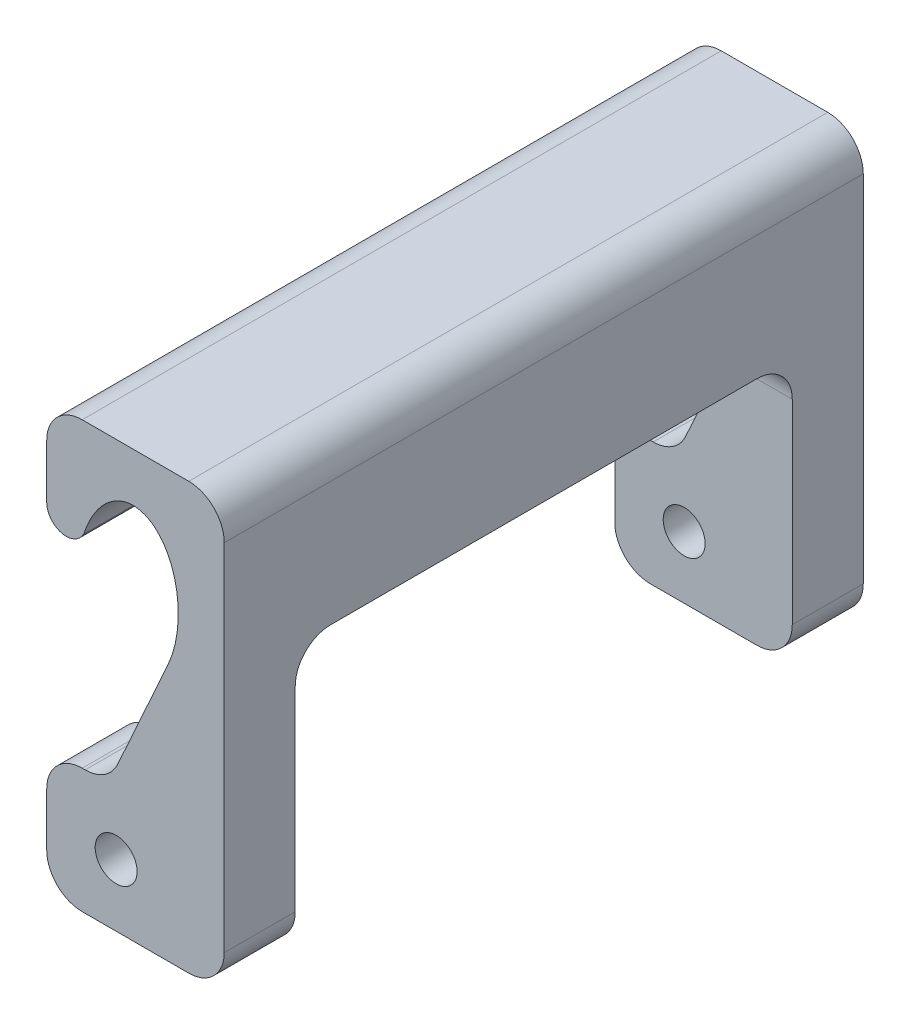
SolidWorks part; units mm, degrees
ref_plane "Front Plane" through (0, 0, 0) normal (0, 0, 1) x (1, 0, 0)
ref_plane "Top Plane" through (0, 0, 0) normal (0, 1, 0) x (1, 0, 0)
ref_plane "Right Plane" through (0, 0, 0) normal (1, 0, 0) x (0, 0, -1)
sketch "Sketch1" plane through (0, 0, 0) normal (0, 0, 1) x (1, 0, 0)
  line L0 (8.6779, 18.3764) -> (5.067, 10.3842)
  line L1 (2.54, 0) -> (10.16, 0)
  line L2 (0, 2.54) -> (0, 6.35)
  line L3 (2.54, 30.48) -> (10.16, 30.48)
  line L4 (12.7, 2.54) -> (12.7, 27.94)
  line L5 (2.7522, 8.89) -> (2.54, 8.89)
  line L6 (0, 24.08) -> (0, 27.94)
  arc A0 (0, 24.08) -> (2.5803, 23.349) centre (1.3937, 24.08) ccw
  arc A1 (2.5803, 23.349) -> (9.3645, 22.7915) centre (5.8307, 21.3468) cw
  arc A2 (5.067, 10.3842) -> (2.7522, 8.89) centre (2.7522, 11.43) cw
  circle A3 centre (4.9655, 4.445) radius 1.5
  arc A4 (10.16, 0) -> (12.7, 2.54) centre (10.16, 2.54) ccw
  arc A5 (10.16, 30.48) -> (12.7, 27.94) centre (10.16, 27.94) cw
  arc A6 (0, 27.94) -> (2.54, 30.48) centre (2.54, 27.94) cw
  arc A7 (2.54, 0) -> (0, 2.54) centre (2.54, 2.54) cw
  arc A8 (2.54, 8.89) -> (0, 6.35) centre (2.54, 6.35) ccw
  ellipse E0 centre (5.8307, 21.3468) end of major axis (6.4063, 26.9833) minor radius 3.5519
  point P9 (0, 0)
  point P16 (0, 0)
  point P20 (12.7, 0)
  point P25 (0, 30.48)
  point P28 (0, 0)
  dimension "D3" = 2.54
  dimension "D5" = 2.54
  dimension "D6" = 3
  dimension "D7" = 2.54
  dimension "D1" = 12.7
  dimension "D2" = 30.48
  dimension "D4" = 19.635
  dimension "D8" = 4.445
  dimension "D9" = 8.89
extrude "Boss-Extrude1" add sketch "Sketch1" along normal blind 45.72 contours A7 L1 A4 L4 A5 L3 A6 L2 A0 A1 L0 A2 L5 A3
sketch "Sketch2" plane through (12.7, 0, 0) normal (1, 0, 0) x (0, 0, -1)
  line L0 (-45.72, 0) -> (0, 0) construction
  line L1 (-40.64, 0) -> (-5.08, 0)
  line L2 (-40.64, 0) -> (-40.64, 16.51)
  line L3 (-38.1, 19.05) -> (-7.62, 19.05)
  line L4 (-5.08, 0) -> (-5.08, 16.51)
  line L5 (-45.72, 2.54) -> (-45.72, 27.94) construction
  line L6 (0, 2.54) -> (0, 27.94) construction
  arc A0 (-7.62, 19.05) -> (-5.08, 16.51) centre (-7.62, 16.51) cw
  arc A1 (-40.64, 16.51) -> (-38.1, 19.05) centre (-38.1, 16.51) cw
  dimension "D4" = 2.54
  dimension "D1" = 5.08
  dimension "D2" = 5.08
  dimension "D3" = 19.05
extrude "Cut-Extrude1" cut sketch "Sketch2" against normal blind 25.4
